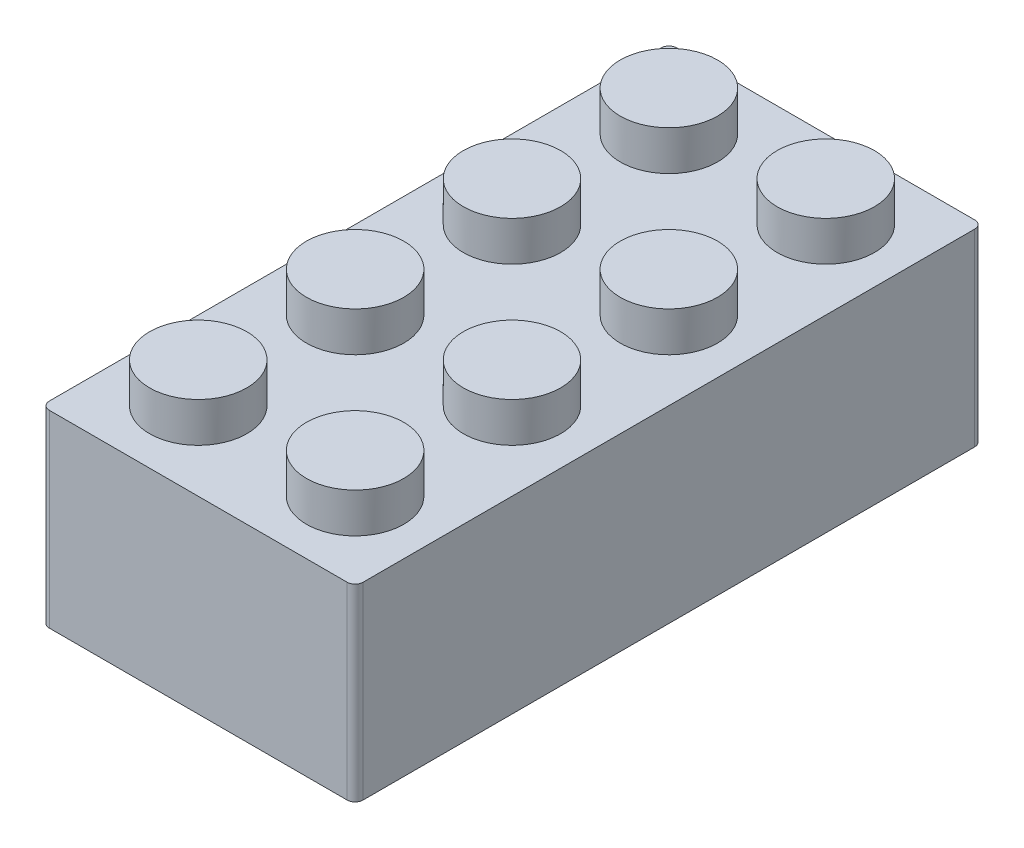
SolidWorks part; units mm, degrees
ref_plane "Front Plane" through (0, 0, 0) normal (0, 0, 1) x (1, 0, 0)
ref_plane "Top Plane" through (0, 0, 0) normal (0, 1, 0) x (1, 0, 0)
ref_plane "Right Plane" through (0, 0, 0) normal (1, 0, 0) x (0, 0, -1)
sketch "stencil" plane through (0, 0, 0) normal (0, 1, 0) x (1, 0, 0)
  line L2 (0, 0) -> (0, 31.6) construction
  line L29 (0, 0) -> (15.8, 0) construction
  line L30 (0, 3.95) -> (15.8, 3.95) construction
  line L31 (0, 7.9) -> (15.8, 7.9) construction
  line L32 (0, 11.85) -> (15.8, 11.85) construction
  line L33 (0, 15.8) -> (15.8, 15.8) construction
  line L34 (0, 19.75) -> (15.8, 19.75) construction
  line L35 (0, 23.7) -> (15.8, 23.7) construction
  line L36 (0, 27.65) -> (15.8, 27.65) construction
  line L37 (0, 31.6) -> (15.8, 31.6) construction
  line L38 (3.95, 0) -> (3.95, 31.6) construction
  line L39 (7.9, 0) -> (7.9, 31.6) construction
  line L40 (11.85, 0) -> (11.85, 31.6) construction
  line L41 (15.8, 0) -> (15.8, 31.6) construction
  line L42 (0, 31.6) -> (0, 0)
  line L43 (0, 0) -> (15.8, 0)
  line L44 (15.8, 0) -> (15.8, 31.6)
  line L45 (15.8, 31.6) -> (0, 31.6)
  circle A26 centre (3.95, 3.95) radius 2.45
  circle A27 centre (11.85, 3.95) radius 2.45
  circle A28 centre (11.85, 11.85) radius 2.45
  circle A29 centre (3.95, 11.85) radius 2.45
  circle A30 centre (11.85, 19.75) radius 2.45
  circle A31 centre (3.95, 19.75) radius 2.45
  circle A32 centre (11.85, 27.65) radius 2.45
  circle A33 centre (3.95, 27.65) radius 2.45
  circle A34 centre (7.9, 7.9) radius 3.25
  circle A35 centre (7.9, 7.9) radius 2.45
  circle A36 centre (7.9, 15.8) radius 2.45
  circle A37 centre (7.9, 15.8) radius 3.25
  circle A38 centre (7.9, 23.7) radius 2.45
  circle A39 centre (7.9, 23.7) radius 3.25
  point P6 (3.95, -15.8)
  point P9 (7.9, -15.8)
  point P10 (7.9, -11.85)
  point P13 (3.95, -7.9)
  point P15 (7.9, -7.9)
  point P17 (7.9, -3.95)
  point P18 (3.95, 0)
  point P21 (7.9, 0)
  point P25 (7.9, 3.95)
  point P27 (3.95, 7.9)
  point P28 (7.9, 7.9)
  point P29 (0, -11.85)
  point P30 (0, -7.9)
  point P31 (0, 3.95)
  point P34 (0, -3.95)
  point P36 (0, 15.8)
  point P37 (0, 23.7)
  point P38 (7.9, 23.7)
  point P39 (15.8, 23.7)
  point P40 (15.8, 15.8)
  point P41 (15.8, 7.9)
  dimension "D7" = 4.9
  dimension "D9" = 6.5
  dimension "D1" = 31.6
  dimension "D2" = 15.8
  dimension "D4" = 3.95
  dimension "D6" = 3.95
  dimension "D8" = 0.8
  dimension "D5" = 9
  dimension "D3" = 5
sketch "Sketch1" plane through (0, 0, 0) normal (0, 1, 0) x (1, 0, 0)
  line L17 (0, 0) -> (15.8, 0)
  line L18 (0, 0) -> (0, 31.6)
  line L19 (0, 31.6) -> (15.8, 31.6)
  line L20 (15.8, 0) -> (15.8, 31.6)
extrude "Boss-Extrude1" add sketch "Sketch1" along normal mid plane 9.5
sketch "Sketch2" plane through (0, 4.75, 0) normal (0, 1, 0) x (1, 0, 0)
  circle A3 centre (3.95, 3.95) radius 2.45
  circle A11 centre (11.85, 3.95) radius 2.45
  circle A12 centre (11.85, 11.85) radius 2.45
  circle A13 centre (3.95, 11.85) radius 2.45
  circle A14 centre (3.95, 19.75) radius 2.45
  circle A15 centre (11.85, 19.75) radius 2.45
  circle A16 centre (3.95, 27.65) radius 2.45
  circle A26 centre (3.95, 27.65) radius 2.45 construction
  circle A27 centre (11.85, 27.65) radius 2.45
extrude "Boss-Extrude2" add sketch "Sketch2" along normal blind 2
sketch "Sketch3" plane through (0, -4.75, 0) normal (0, -1, 0) x (1, 0, 0)
  line L0 (0, -15.8) -> (15.8, -15.8) construction
  line L5 (14.3, -30.1) -> (1.5, -30.1)
  line L7 (14.3, -30.1) -> (14.3, -1.5)
  line L15 (14.3, -1.5) -> (1.5, -1.5)
  line L16 (1.5, -30.1) -> (1.5, -1.5)
  line L17 (7.9, -1.5) -> (7.9, -30.1) construction
  line L18 (14.3, -15.8) -> (1.5, -15.8) construction
  line L19 (0, 0) -> (15.8, 0) construction
  line L20 (0, -31.6) -> (0, 0) construction
  point P0 (7.9, -15.8)
  dimension "D1" = 1.5
  dimension "D2" = 1.5
extrude "Cut-Extrude1" cut sketch "Sketch3" against normal blind 4
sketch "Sketch4" plane through (0, -0.75, 0) normal (0, -1, 0) x (1, 0, 0)
  line L0 (0, -7.9) -> (15.8, -7.9) construction
  line L1 (0, -15.8) -> (15.8, -15.8) construction
  line L2 (0, -23.7) -> (15.8, -23.7) construction
  circle A2 centre (7.9, -7.9) radius 3.25
  circle A3 centre (7.9, -7.9) radius 2.45
  circle A6 centre (7.9, -15.8) radius 3.25
  circle A7 centre (7.9, -15.8) radius 2.45
  circle A10 centre (7.9, -23.7) radius 3.25
  circle A11 centre (7.9, -23.7) radius 2.45
  circle A20 centre (7.9, -23.7) radius 2.45 construction
  circle A21 centre (7.9, -23.7) radius 3.25 construction
extrude "Boss-Extrude3" add sketch "Sketch4" along normal up to surface (4 mm away) up to face at (7.9, -4.75, -15.8)
fillet "Fillet1" radius 0.4 4 edges at (0, 0, -31.6) (15.8, 0, -31.6) (15.8, 0, 0) (0, 0, 0)
equation "\"t\"= 0'tolerance"
equation "\"D1@Sketch3\"= 1.5 - \"t\""
equation "\"D2@Sketch3\"=1.5-\"t\""
equation "\"D1@stencil\"=31.60mm-\"t\""
equation "\"D9@stencil\"=6.5-\"t\""
equation "\"D2@stencil\"=15.80-\"t\""
equation "\"D1@Boss-Extrude1\"=9.5-\"t\""
